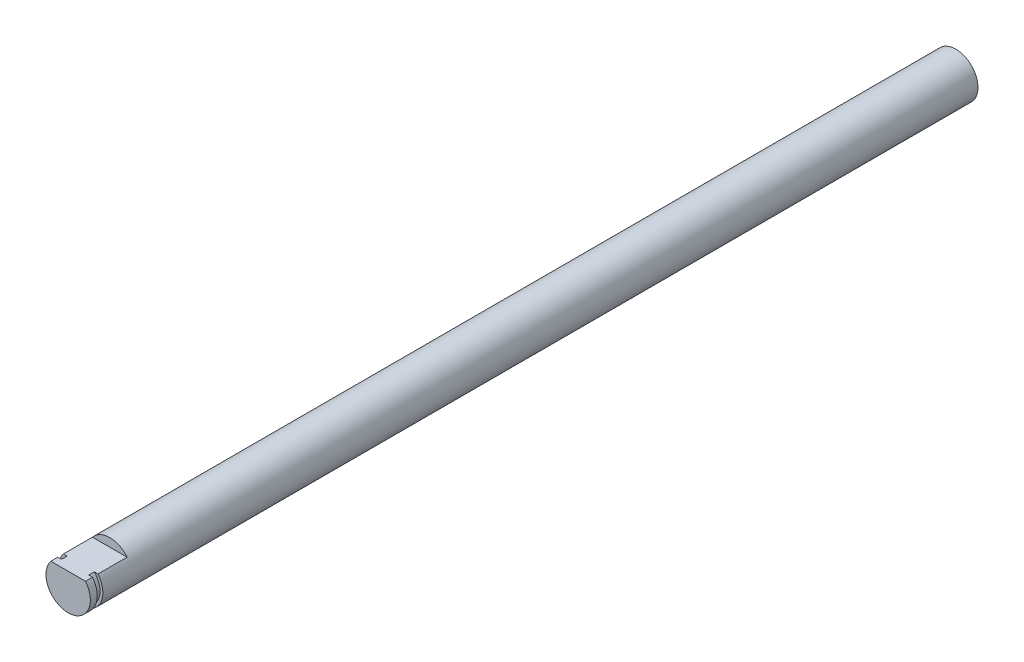
SolidWorks part; units mm, degrees
ref_plane "Front Plane" through (0, 0, 0) normal (0, 0, 1) x (1, 0, 0)
ref_plane "Top Plane" through (0, 0, 0) normal (0, 1, 0) x (1, 0, 0)
ref_plane "Right Plane" through (0, 0, 0) normal (1, 0, 0) x (0, 0, -1)
sketch "Sketch1" plane through (0, 0, 0) normal (0, 0, 1) x (1, 0, 0)
  circle A0 centre (0, 0) radius 4
  dimension "D1" = 8
extrude "Boss-Extrude1" add sketch "Sketch1" along normal blind 160
sketch "Sketch2" plane through (0, 0, 160) normal (0, 0, 1) x (1, 0, 0)
  line L0 (3.1225, 2.5) -> (-3.1225, 2.5)
  circle A1 centre (0, 0) radius 4
  arc A2 (3.1225, 2.5) -> (-3.1225, 2.5) centre (0, 0) ccw
  dimension "D2" = 2.5
  dimension "D1" = 0
extrude "Cut-Extrude1" cut sketch "Sketch2" against normal blind 7.5
ref_plane "Plane1" through (0, 0, 158.75) normal (0, 0, 1) x (1, 0, 0)
sketch "Sketch3" plane through (0, 0, 158.75) normal (0, 0, 1) x (1, 0, 0)
  circle A0 centre (0, 0) radius 4
  circle A1 centre (0, 0) radius 3.5
extrude "Cut-Extrude2" cut sketch "Sketch3" against normal blind 1
